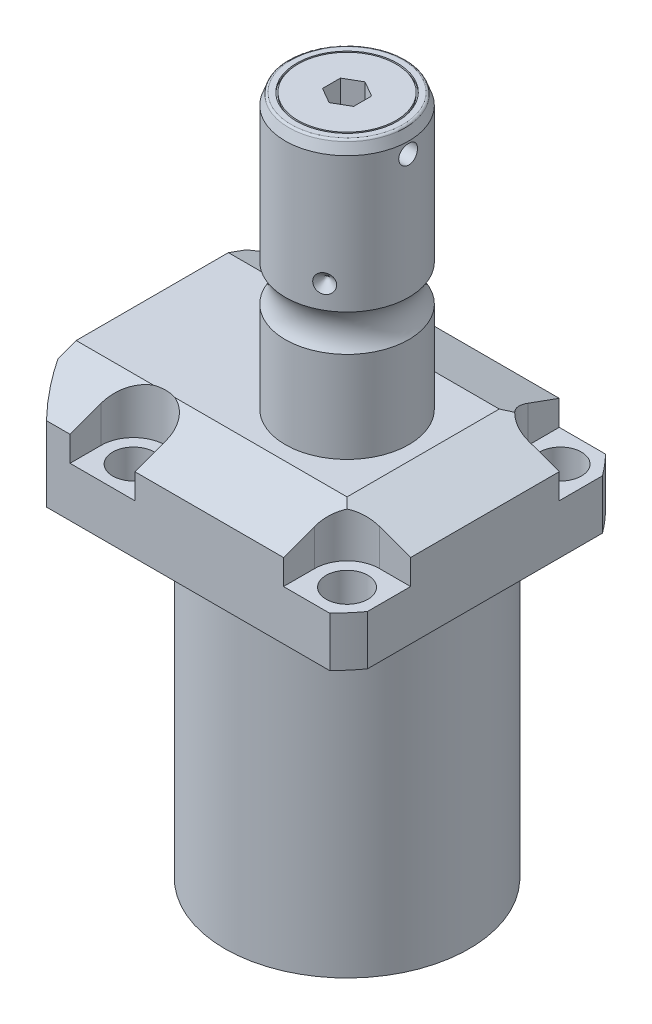
SolidWorks part; units mm, degrees
material "Alloy Steel"
ref_plane "Front Plane" through (0, 0, 0) normal (0, 0, 1) x (1, 0, 0)
ref_plane "Top Plane" through (0, 0, 0) normal (0, 1, 0) x (1, 0, 0)
ref_plane "Right Plane" through (0, 0, 0) normal (1, 0, 0) x (0, 0, -1)
sketch "Sketch1" plane through (0, 0, 0) normal (0, -1, 0) x (0, 0, 1)
  line L0 (-35.433, 50.063) -> (35.433, 50.063)
  line L1 (35.433, 50.063) -> (35.433, -35.433)
  line L2 (35.433, -35.433) -> (-35.433, -35.433)
  line L3 (-35.433, -35.433) -> (-35.433, 50.063)
  line L4 (0, 0) -> (0, -60.6467) construction
  dimension "D1" = 35.433
  dimension "D2" = 85.496
  dimension "D3" = 70.866
extrude "Extrude1" add sketch "Sketch1" against normal blind 104.4448
sketch "Sketch2" plane through (0, 0, 0) normal (0, -1, 0) x (1, 0, 0)
  circle A0 centre (-5.4102, 0) radius 50.8
  dimension "D1" = 101.6
  dimension "D2" = 5.4102
extrude "Cut-Extrude1" cut sketch "Sketch2" against normal through all flip side to cut
sketch "Sketch3" plane through (0, 0, 0) normal (1, 0, 0) x (0, 0, -1)
  line L0 (31.3945, 0) -> (31.3945, 79.4258)
  line L1 (31.3945, 79.4258) -> (76.5937, 79.4258)
  line L2 (76.5937, 79.4258) -> (76.5937, 0)
  line L3 (76.5937, 0) -> (31.3945, 0)
  line L4 (0, -93.345) -> (0, 4.445) construction
  line L5 (24.2233, 0) -> (-24.2233, 0) construction
  dimension "D1" = 62.789
  dimension "D2" = 153.1874
  dimension "D3" = 79.4258
revolve "Cut-Revolve1" cut sketch "Sketch3" angle 360 about L4
fillet "Fillet1" radius 0.381 1 edges at (0, 79.4258, -31.3945)
sketch "Sketch4" plane through (0, 104.4448, 0) normal (0, 1, 0) x (-1, 0, 0)
  line L0 (-35.433, -30.2072) -> (-35.433, 30.2072) construction
  line L1 (41.8127, 35.433) -> (-30.9923, 35.433) construction
  line L2 (-19.1008, -35.433) -> (-19.1008, -27.432)
  line L3 (-35.433, -35.433) -> (-19.1008, -35.433)
  line L4 (-35.433, -19.1008) -> (-35.433, -35.433)
  line L5 (-27.432, -19.1008) -> (-35.433, -19.1008)
  line L6 (35.7632, -35.433) -> (19.1008, -35.433)
  line L7 (19.1008, 35.433) -> (19.1008, 27.432)
  line L8 (35.7632, 35.433) -> (35.7632, 27.432)
  line L9 (35.7632, 35.433) -> (19.1008, 35.433)
  line L10 (-27.432, 19.1008) -> (-35.433, 19.1008)
  line L11 (-35.433, 19.1008) -> (-35.433, 35.433)
  line L12 (-35.433, 35.433) -> (-19.1008, 35.433)
  line L13 (-19.1008, 35.433) -> (-19.1008, 27.432)
  line L14 (-48.9217, 0) -> (49.4551, 0) construction
  line L15 (35.7632, -35.433) -> (35.7632, -27.432)
  line L16 (19.1008, -35.433) -> (19.1008, -27.432)
  arc A0 (19.1008, -27.432) -> (35.7632, -27.432) centre (27.432, -27.432) cw
  arc A1 (-27.432, -19.1008) -> (-19.1008, -27.432) centre (-27.432, -27.432) cw
  arc A2 (-27.432, 19.1008) -> (-19.1008, 27.432) centre (-27.432, 27.432) ccw
  arc A3 (19.1008, 27.432) -> (35.7632, 27.432) centre (27.432, 27.432) ccw
  dimension "D2" = 8.3312
  dimension "D1" = 27.432
  dimension "D3" = 27.432
  dimension "D4" = 54.864
extrude "Cut-Extrude2" cut sketch "Sketch4" against normal blind 12.243
sketch "Sketch5" plane through (0, 0, 0) normal (1, 0, 0) x (0, 0, -1)
  line L0 (-19.558, 104.4448) -> (-35.433, 98.6668)
  line L1 (0, 0) -> (0, 154.1081) construction
  line L2 (-19.558, 104.4448) -> (-35.433, 104.4448)
  line L3 (-35.433, 104.4448) -> (-35.433, 98.6668)
  dimension "D1" = 15.875
  dimension "D2" = 20
extrude "Cut-Extrude9" cut sketch "Sketch5" against normal through all and the other way through all
mirror "Mirror1" about plane through (0, 0, 0) normal (0, 0, 1) of "Cut-Extrude9"
sketch "Sketch9" plane through (0, 0, 0) normal (0, 0, 1) x (1, 0, 0)
  line L0 (19.558, 104.4448) -> (35.433, 98.6668)
  line L1 (35.433, 98.6668) -> (35.433, 104.4448)
  line L2 (35.433, 104.4448) -> (19.558, 104.4448)
  dimension "D1" = 15.875
  dimension "D2" = 20
extrude "Cut-Extrude7" cut sketch "Sketch9" against normal through all and the other way through all
ref_plane "Plane14" through (-35.0774, 0, 0) normal (1, 0, 0) x (0, 0, -1)
sketch "Sketch20" plane through (-35.0774, 88.9, -18.1102) normal (1, 0, 0) x (0, 1, 0)
  line L0 (-88.9, 18.1102) -> (39.8401, 18.1102) construction
  line L1 (-7.2797, 32.639) -> (36.9042, 32.639) construction
  line L2 (-9.4742, 38.3413) -> (-8.0264, 38.3413)
  line L3 (-9.4742, -6.1131) -> (-9.4742, 42.3335) construction
  line L4 (-8.0264, 38.3413) -> (-8.0264, 35.8902)
  line L5 (-8.0264, 35.8902) -> (-7.0104, 35.8902)
  line L6 (-7.0104, 35.8902) -> (-7.0104, 33.8836)
  line L7 (-7.0104, 33.8836) -> (3.9624, 33.8836)
  line L8 (3.9624, 33.8836) -> (3.9624, 32.639)
  line L9 (3.9624, 32.639) -> (-9.4742, 32.639)
  line L10 (-9.4742, 38.3413) -> (-9.4742, 32.639)
  dimension "D1" = 14.5288
  dimension "D2" = 11.4046
  dimension "D3" = 1.4478
  dimension "D4" = 6.5024
  dimension "D5" = 1.016
  dimension "D6" = 2.4892
  dimension "D7" = 10.9728
revolve "Cut-Revolve4" cut sketch "Sketch20" angle 360 about L1
mirror "Mirror10" about plane through (0, 0, 0) normal (0, 0, 1) of "Cut-Revolve4"
sketch "Sketch10" plane through (-35.0774, 88.9, -18.1102) normal (1, 0, 0) x (0, 1, 0)
  line L0 (-1.0325, 3.5814) -> (1.5659, 3.5814) construction
  line L1 (3.9624, 4.826) -> (-7.0104, 4.826) construction
  line L2 (-7.0104, 2.3368) -> (3.9624, 2.3368) construction
  line L4 (-9.4742, -12.097) -> (-9.4742, 48.3174) construction
  circle A0 centre (-9.2075, 8.1026) radius 1.1811
  dimension "D1" = 2.3622
  dimension "D2" = 0.2667
  dimension "D3" = 9.0424
revolve "Revolve4" add sketch "Sketch10" angle 360 about L0
mirror "Mirror12" about plane through (0, 0, 0) normal (0, 0, 1) of bodies 135
sketch "Sketch15" plane through (0, 0, 0) normal (1, 0, 0) x (0, 0, -1)
  line L0 (0, 104.4448) -> (15.875, 104.4448)
  line L1 (15.875, 104.4448) -> (15.875, 127.8287)
  line L2 (15.875, 137.2429) -> (15.875, 172.0328)
  line L3 (14.8118, 174.9538) -> (0, 174.9538)
  line L4 (0, 174.9538) -> (0, 104.4448)
  line L5 (0, 250.2908) -> (0, 28.9095) construction
  line L6 (19.558, 104.4448) -> (-19.558, 104.4448) construction
  line L7 (14.8118, 174.9538) -> (15.875, 172.0328)
  arc A0 (15.875, 137.2429) -> (15.875, 127.8287) centre (22.2504, 132.5358) ccw
  dimension "D2" = 20
  dimension "D4" = 7.9248
  dimension "D6" = 28.6512
  dimension "D1" = 95.528
  dimension "D3" = 31.75
  dimension "D5" = 42.418
  dimension "D7" = 2.921
revolve "Revolve3" add sketch "Sketch15" angle 360 about L5
hole_wizard "Hole1" positions "Sketch18" profile "Sketch17" legacy end condition up to next
sketch "Sketch18" plane through (0, 92.2018, 0) normal (0, 1, 0) x (-1, 0, 0)
  arc A0 (35.7632, -27.432) -> (19.1008, -27.432) centre (27.432, -27.432) ccw construction
  arc A1 (19.1008, 27.432) -> (35.7632, 27.432) centre (27.432, 27.432) ccw construction
  arc A2 (-27.432, 19.1008) -> (-19.1008, 27.432) centre (-27.432, 27.432) ccw construction
  arc A3 (-19.1008, -27.432) -> (-27.432, -19.1008) centre (-27.432, -27.432) ccw construction
  point P0 (-27.432, -27.432)
  point P1 (-27.432, 27.432)
  point P3 (27.432, 27.432)
  point P5 (27.432, -27.432)
sketch "Sketch17" plane through (27.432, 92.2018, -27.432) normal (1, 0, 0) x (0, 0, 1)
  line L0 (0, 0) -> (0, 12.776)
  line L1 (0, 12.776) -> (5.3594, 12.776)
  line L2 (5.3594, 12.776) -> (5.3594, 0)
  line L3 (5.3594, 0) -> (0, 0)
  line L4 (0, 110) -> (0, -10) construction
  dimension "Diameter" = 10.7188
  dimension "Depth" = 12.776
chamfer "Chamfer1" distance 0.635 angle 45 2 edges at (-35.0774, 81.8896, 13.2842) (-35.0774, 81.8896, -13.2842)
ref_plane "Plane15" through (0, 91.9226, 0) normal (0, -1, 0) x (1, 0, 0)
sketch "Sketch21" plane through (0, 91.9226, 0) normal (0, -1, 0) x (1, 0, 0)
  line L0 (-57.5495, -12.9794) -> (-2.9353, -12.9794) construction
  line L1 (-50.063, -2.5019) -> (-49.809, -2.5019)
  line L2 (-49.809, -2.5019) -> (-49.809, -6.7564)
  line L3 (-49.809, -6.7564) -> (-47.2563, -7.4404)
  line L4 (-46.6957, -8.001) -> (-30.759, -8.001)
  line L5 (-30.759, -8.001) -> (-30.759, -12.9794)
  line L6 (-30.759, -12.9794) -> (-50.063, -12.9794)
  line L7 (-50.063, 24.2233) -> (-50.063, -24.2233) construction
  line L8 (-50.063, -12.9794) -> (-50.063, -2.5019)
  line L9 (-47.2563, -7.4404) -> (-46.6957, -8.001)
  dimension "D1" = 12.9794
  dimension "D2" = 0.254
  dimension "D3" = 20.955
  dimension "D4" = 15
  dimension "D5" = 12.446
  dimension "D6" = 9.9568
  dimension "D7" = 45
  dimension "D8" = 2.5527
revolve "Cut-Revolve5" cut sketch "Sketch21" angle 360 about L0
mirror "Mirror13" about plane through (0, 0, 0) normal (0, 0, 1) of "Cut-Revolve5"
sketch "Sketch22" plane through (-49.809, 0, 0) normal (-1, 0, 0) x (0, 0, 1)
  circle A0 centre (-12.9794, 91.9226) radius 6.35
  dimension "D1" = 12.7
extrude "Extrude2" add sketch "Sketch22" along normal blind 1.651
fillet "Fillet2" radius 0.635 1 edges at (0, 174.9538, 14.8118)
sketch "Sketch24" plane through (0, 174.9538, 0) normal (0, 1, 0) x (1, 0, 0)
  circle A0 centre (0, 0) radius 12.954
  circle A1 centre (0, 0) radius 12.573
  dimension "D1" = 25.908
  dimension "D2" = 25.146
extrude "Cut-Extrude10" cut sketch "Sketch24" against normal blind 0.5
sketch "Sketch25" plane through (0, 174.9538, 0) normal (0, 1, 0) x (1, 0, 0)
  line L1 (4, -2.3094) -> (4, 2.3094)
  line L2 (4, 2.3094) -> (0, 4.6188)
  line L3 (0, 4.6188) -> (-4, 2.3094)
  line L4 (-4, 2.3094) -> (-4, -2.3094)
  line L5 (-4, -2.3094) -> (0, -4.6188)
  line L6 (0, -4.6188) -> (4, -2.3094)
  circle A0 centre (0, 0) radius 4 construction
  dimension "D1" = 8
extrude "Cut-Extrude11" cut sketch "Sketch25" against normal blind 8
sketch "Sketch26" plane through (0, 0, 0) normal (0, 0, 1) x (1, 0, 0)
  line L0 (-39.772, 143.2038) -> (35.3173, 143.2038) construction
  line L1 (-15.875, 145.6168) -> (-13.462, 143.2038)
  line L2 (-15.875, 172.0328) -> (-15.875, 137.2429) construction
  line L3 (-13.462, 143.2038) -> (-15.875, 143.2038)
  line L4 (-15.875, 143.2038) -> (-15.875, 145.6168)
  arc A0 (-15.875, 127.8287) -> (-15.875, 137.2429) centre (-22.2504, 132.5358) ccw construction
  dimension "D1" = 45
  dimension "D2" = 4.826
  dimension "D3" = 10.668
revolve "Cut-Revolve7" cut sketch "Sketch26" angle 360 about L0
pattern_circular "CirPattern1" count 3 over 360 about axis through (0, 250.2908, 0) along (0, 1, 0) of "Cut-Revolve7"
sketch "Sketch27" plane through (0, 0, 0) normal (0, 0, 1) x (1, 0, 0)
  line L0 (5.3741, 169.1118) -> (21.6654, 169.1118) construction
  line L1 (15.875, 137.2429) -> (15.875, 172.0328) construction
  line L2 (15.875, 171.5248) -> (12.065, 171.5248)
  line L3 (15.875, 171.5248) -> (15.875, 169.1118)
  line L4 (15.875, 169.1118) -> (12.065, 169.1118)
  line L5 (12.065, 171.5248) -> (12.065, 169.1118)
  line L6 (12.573, 174.9538) -> (-12.573, 174.9538) construction
  dimension "D1" = 4.826
  dimension "D2" = 3.81
  dimension "D3" = 5.842
revolve "Cut-Revolve8" cut sketch "Sketch27" angle 360 about L0
chamfer "Chamfer2" distance 1.016 angle 45 1 edges at (-51.46, 91.9226, -6.6294)
